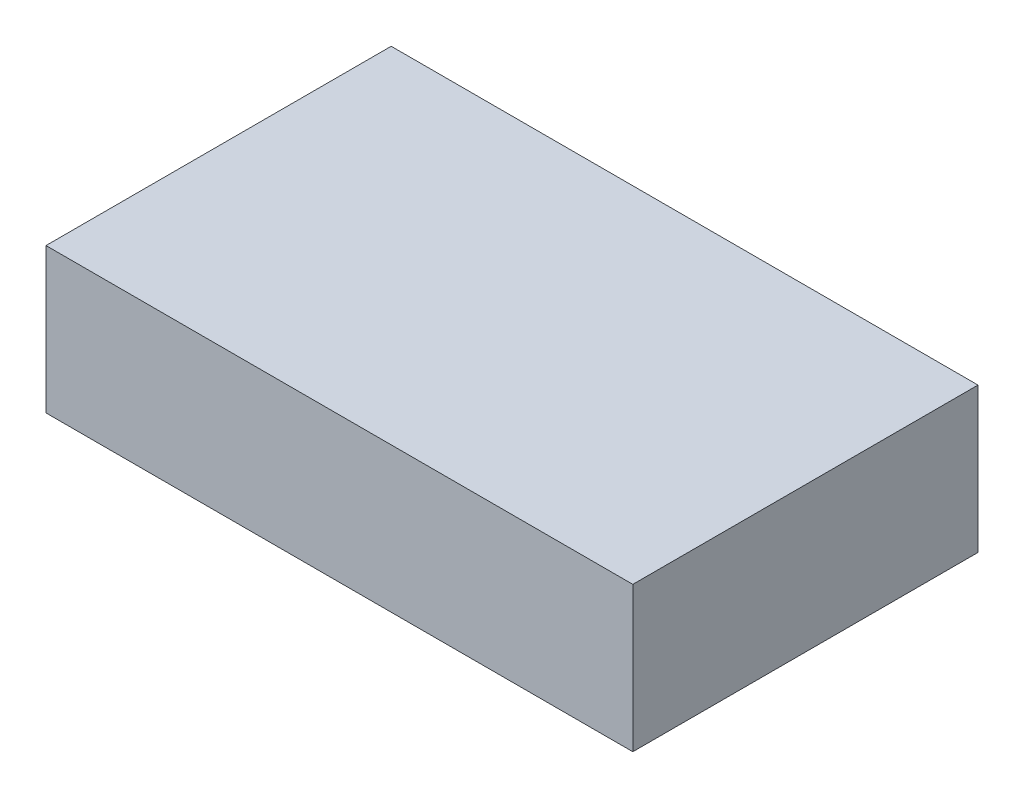
SolidWorks part; units mm, degrees
ref_plane "Front Plane" through (0, 0, 0) normal (0, 0, 1) x (1, 0, 0)
ref_plane "Top Plane" through (0, 0, 0) normal (0, 1, 0) x (1, 0, 0)
ref_plane "Right Plane" through (0, 0, 0) normal (1, 0, 0) x (0, 0, -1)
sketch "Sketch2" plane through (0, 0, 0) normal (0, 1, 0) x (1, 0, 0)
  line L1 (-42.5, -25) -> (42.5, -25)
  line L2 (-42.5, -25) -> (-42.5, 25)
  line L3 (-42.5, 25) -> (42.5, 25)
  line L4 (42.5, -25) -> (42.5, 25)
  line L5 (-42.5, -25) -> (42.5, 25) construction
  line L6 (-42.5, 25) -> (42.5, -25) construction
  point P0 (0, 0)
  dimension "D1" = 85
  dimension "D2" = 50
extrude "Boss-Extrude1" add sketch "Sketch2" along normal mid plane 21
